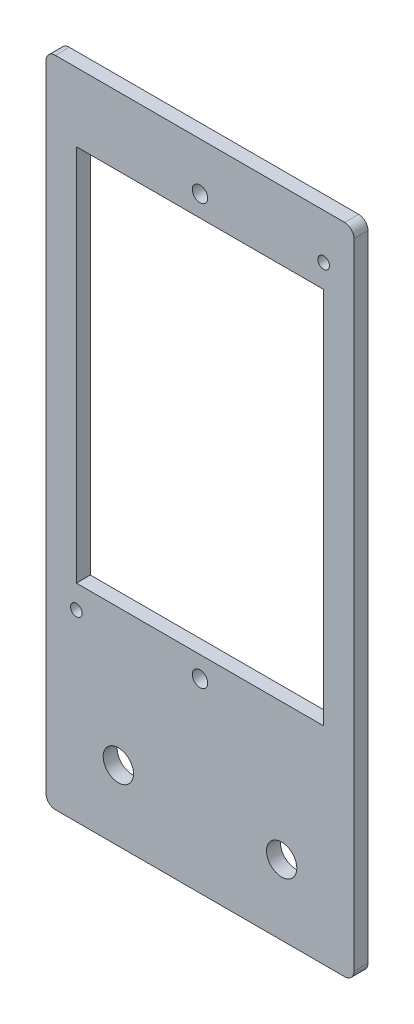
SolidWorks part; units mm, degrees
ref_plane "Front Plane" through (0, 0, 0) normal (0, 0, 1) x (1, 0, 0)
ref_plane "Top Plane" through (0, 0, 0) normal (0, 1, 0) x (1, 0, 0)
ref_plane "Right Plane" through (0, 0, 0) normal (1, 0, 0) x (0, 0, -1)
sketch "Sketch1" plane through (0, 0, 0) normal (0, 0, 1) x (1, 0, 0)
  line L1 (-10.8552, 25.3327) -> (55.1448, 25.3327)
  line L2 (-10.8552, 25.3327) -> (-10.8552, -114.6673)
  line L3 (-10.8552, -114.6673) -> (55.1448, -114.6673)
  line L4 (55.1448, 25.3327) -> (55.1448, -114.6673)
  line L5 (-4.3552, 10.6327) -> (48.6448, 10.6327)
  line L6 (-4.3552, 10.6327) -> (-4.3552, -70.3673)
  line L7 (-4.3552, -70.3673) -> (48.6448, -70.3673)
  line L8 (48.6448, 10.6327) -> (48.6448, -70.3673)
  circle A0 centre (4.6448, -99.6673) radius 3.25
  circle A1 centre (39.6448, -99.6673) radius 3.25
  point P12 (0, 0)
  dimension "D7" = 6.5
  dimension "D8" = 15
  dimension "D9" = 35
  dimension "D10" = 15.5
  dimension "D1" = 66
  dimension "D2" = 140
  dimension "D3" = 6.5
  dimension "D4" = 44.3
  dimension "D5" = 125.3
  dimension "D6" = 53
extrude "Boss-Extrude1" add sketch "Sketch1" along normal blind 3
fillet "Fillet1" radius 2 4 edges at (-10.8552, -114.6673, 1.5) (55.1448, -114.6673, 1.5) (55.1448, 25.3327, 1.5) (-10.8552, 25.3327, 1.5)
hole_wizard "M4x0.7 Tapped Hole1" positions "Sketch2" profile "Sketch3" tap size "M4x0.7" standard "ANSI Metric" end condition through all
sketch "Sketch2" plane through (0, 0, 3) normal (0, 0, 1) x (1, 0, 0)
  line L0 (-8.8552, -114.6673) -> (53.1448, -114.6673) construction
  line L1 (-10.8552, 23.3327) -> (-10.8552, -112.6673) construction
  point P0 (22.1448, 15.1327)
  point P2 (22.1448, -74.8673)
  point P3 (0, 0)
  point P10 (0, 0)
  dimension "D1" = 39.8
  dimension "D2" = 33
  dimension "D3" = 129.8
sketch "Sketch3" plane through (22.1448, 15.1327, 3) normal (1, 0, 0) x (0, -1, 0)
  line L0 (0, 0) -> (0, 3)
  line L1 (0, 3) -> (1.65, 3)
  line L2 (1.65, 3) -> (1.65, 0)
  line L5 (1.65, 0) -> (0, 0)
  line L11 (0, -6.35) -> (0, 107.95) construction
  dimension "Thru Tap Drill Dia." = 3.3
  dimension "Thru Tap Drill Depth" = 3
cosmetic thread "Hole Thread1" parameters "D2"=4
cosmetic thread "Hole Thread2" parameters "D2"=4
hole_wizard "M3x0.5 Tapped Hole1" positions "Sketch4" profile "Sketch5" tap size "M3x0.5" standard "ANSI Metric" end condition through all
sketch "Sketch4" plane through (0, 0, 3) normal (0, 0, 1) x (1, 0, 0)
  line L0 (-8.8552, -114.6673) -> (53.1448, -114.6673) construction
  line L1 (-10.8552, 23.3327) -> (-10.8552, -112.6673) construction
  point P0 (48.6448, 15.6327)
  point P2 (-4.3552, -75.3673)
  point P5 (0, 0)
  dimension "D1" = 130.3
  dimension "D2" = 59.5
  dimension "D3" = 6.5
  dimension "D4" = 39.3
sketch "Sketch5" plane through (48.6448, 15.6327, 3) normal (1, 0, 0) x (0, -1, 0)
  line L0 (0, 0) -> (0, 3)
  line L1 (0, 3) -> (1.25, 3)
  line L2 (1.25, 3) -> (1.25, 0)
  line L5 (1.25, 0) -> (0, 0)
  line L11 (0, -6.35) -> (0, 107.95) construction
  dimension "Thru Tap Drill Dia." = 2.5
  dimension "Thru Tap Drill Depth" = 3
cosmetic thread "Hole Thread3" parameters "D2"=3
cosmetic thread "Hole Thread4" parameters "D2"=3
